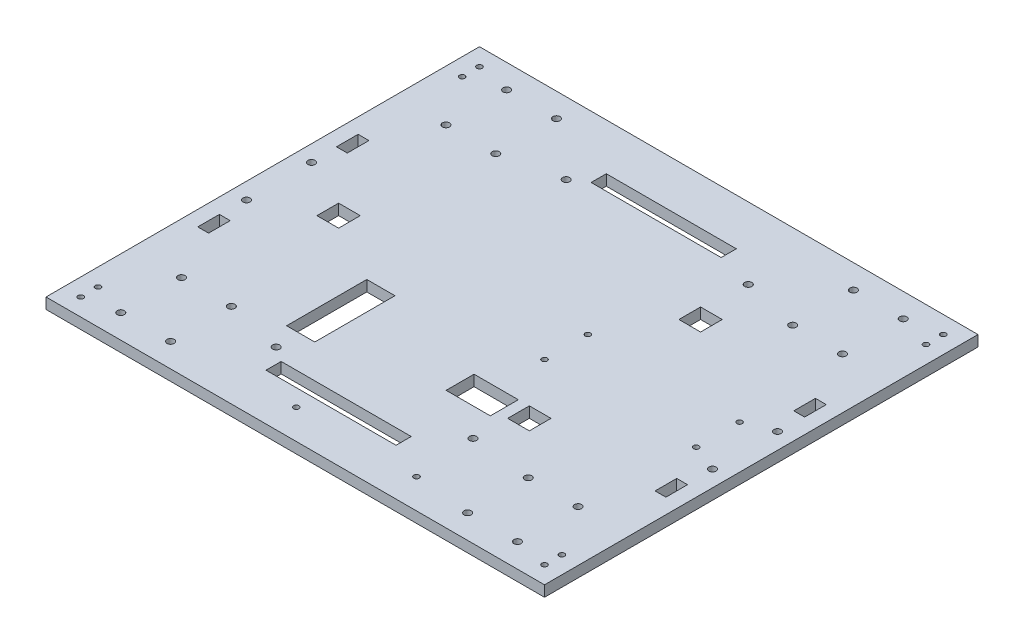
SolidWorks part; units mm, degrees
material "1060 Alloy"
ref_plane "Ebene vorne" through (0, 0, 0) normal (0, 0, 1) x (1, 0, 0)
ref_plane "Ebene oben" through (0, 0, 0) normal (0, 1, 0) x (1, 0, 0)
ref_plane "Ebene rechts" through (0, 0, 0) normal (1, 0, 0) x (0, 0, -1)
sketch "Sketch1" plane through (0, 0, 0) normal (0, 1, 0) x (1, 0, 0)
  line L1 (-110, -91.3059) -> (120, -91.3059)
  line L2 (-110, -91.3059) -> (-110, 108.6941)
  line L3 (-110, 108.6941) -> (120, 108.6941)
  line L4 (120, -91.3059) -> (120, 108.6941)
  line L5 (-110, -91.3059) -> (120, 108.6941) construction
  line L6 (-110, 108.6941) -> (120, -91.3059) construction
  point P0 (5, 8.6941)
  dimension "D1" = 200
  dimension "D2" = 230
extrude "Extrude1" add sketch "Sketch1" along normal blind 5 contours L2 L1 L4 L3
sketch "Sketch3" plane through (0, 5, 0) normal (0, 1, 0) x (1, 0, 0)
  line L0 (-110, -91.3059) -> (-110, 108.6941) construction
  line L1 (-100, 108.6941) -> (-50, 108.6941) construction
  line L2 (-100, 108.6941) -> (-100, 18.6941) construction
  line L3 (-100, 18.6941) -> (-50, 18.6941) construction
  line L4 (-50, 108.6941) -> (-50, 18.6941) construction
  line L5 (-110, 108.6941) -> (120, 108.6941) construction
  line L6 (-110, -91.3059) -> (120, -91.3059) construction
  line L7 (-100, -91.3059) -> (-50, -91.3059) construction
  line L8 (-100, -91.3059) -> (-100, -1.3059) construction
  line L9 (-100, -1.3059) -> (-50, -1.3059) construction
  line L10 (-50, -91.3059) -> (-50, -1.3059) construction
  line L11 (120, -91.3059) -> (120, 108.6941) construction
  line L12 (60, -1.3059) -> (110, -1.3059) construction
  line L13 (60, -1.3059) -> (60, -91.3059) construction
  line L14 (60, -91.3059) -> (110, -91.3059) construction
  line L15 (110, -1.3059) -> (110, -91.3059) construction
  line L17 (60, 108.6941) -> (110, 108.6941) construction
  line L18 (60, 108.6941) -> (60, 18.6941) construction
  line L19 (60, 18.6941) -> (110, 18.6941) construction
  line L20 (110, 108.6941) -> (110, 18.6941) construction
  line L21 (-95, 88.6941) -> (105, 88.6941) construction
  line L22 (-95, 88.6941) -> (-95, -71.3059) construction
  line L23 (-95, -71.3059) -> (105, -71.3059) construction
  line L24 (105, 88.6941) -> (105, -71.3059) construction
  line L29 (-30, 80.1941) -> (30, 80.1941)
  line L30 (-30, 80.1941) -> (-30, 87.1941)
  line L31 (-30, 87.1941) -> (30, 87.1941)
  line L32 (30, 80.1941) -> (30, 87.1941)
  line L33 (-30, 80.1941) -> (30, 87.1941) construction
  line L34 (-30, 87.1941) -> (30, 80.1941) construction
  line L35 (-30, -69.8059) -> (30, -69.8059)
  line L36 (-30, -69.8059) -> (-30, -62.8059)
  line L37 (-30, -62.8059) -> (30, -62.8059)
  line L38 (30, -69.8059) -> (30, -62.8059)
  line L39 (-30, -69.8059) -> (30, -62.8059) construction
  line L40 (-30, -62.8059) -> (30, -69.8059) construction
  line L41 (-43, -10.3059) -> (-30, -10.3059)
  line L42 (-43, -10.3059) -> (-43, -47.3059)
  line L43 (-43, -47.3059) -> (-30, -47.3059)
  line L44 (-30, -10.3059) -> (-30, -47.3059)
  circle A0 centre (-86.5, 97.6941) radius 1.65
  circle A1 centre (-63.5, 97.6941) radius 1.65
  circle A2 centre (-86.5, 69.6941) radius 1.65
  circle A3 centre (-63.5, 69.6941) radius 1.65
  circle A4 centre (-86.5, -52.3059) radius 1.65
  circle A5 centre (-63.5, -52.3059) radius 1.65
  circle A6 centre (-86.5, -80.3059) radius 1.65
  circle A7 centre (-63.5, -80.3059) radius 1.65
  circle A8 centre (73.5, -52.3059) radius 1.65
  circle A9 centre (96.5, -52.3059) radius 1.65
  circle A10 centre (73.5, -80.3059) radius 1.65
  circle A11 centre (96.5, -80.3059) radius 1.65
  circle A12 centre (73.5, 97.6941) radius 1.65
  circle A13 centre (96.5, 97.6941) radius 1.65
  circle A14 centre (73.5, 69.6941) radius 1.65
  circle A15 centre (96.5, 69.6941) radius 1.65
  circle A17 centre (-36.9, -58.2059) radius 1.65
  circle A18 centre (-36.9, 75.5941) radius 1.65
  circle A19 centre (47, 75.6941) radius 1.65
  circle A20 centre (45, -49.3059) radius 1.65
  point P68 (0, 83.6941)
  point P73 (0, -66.3059)
  dimension "D5" = 3.3
  dimension "D7" = 3.3
  dimension "D11" = 3.3
  dimension "D12" = 3.3
  dimension "D18" = 3.3
  dimension "D54" = 3.3
  dimension "D57" = 3.3
  dimension "D62" = 3.3
  dimension "D63" = 3.3
  dimension "D17" = 3.3
  dimension "D43" = 3.3
  dimension "D47" = 3.3
  dimension "D74" = 3.3
  dimension "D75" = 3.3
  dimension "D76" = 3.3
  dimension "D77" = 3.3
  dimension "D78" = 3.3
  dimension "D79" = 3.3
  dimension "D80" = 3.3
  dimension "D81" = 3.3
  dimension "D1" = 90
  dimension "D2" = 50
  dimension "D3" = 10
  dimension "D6" = 13.5
  dimension "D8" = 13.5
  dimension "D9" = 11
  dimension "D10" = 11
  dimension "D13" = 28
  dimension "D14" = 28
  dimension "D15" = 90
  dimension "D16" = 50
  dimension "D19" = 23
  dimension "D20" = 28
  dimension "D21" = 28
  dimension "D22" = 23
  dimension "D23" = 13.5
  dimension "D24" = 11
  dimension "D25" = 11
  dimension "D26" = 90
  dimension "D27" = 50
  dimension "D28" = 10
  dimension "D29" = 23
  dimension "D30" = 28
  dimension "D31" = 28
  dimension "D32" = 23
  dimension "D33" = 11
  dimension "D34" = 11
  dimension "D35" = 13.5
  dimension "D36" = 13.5
  dimension "D37" = 13.5
  dimension "D38" = 23
  dimension "D39" = 23
  dimension "D40" = 28
  dimension "D41" = 28
  dimension "D42" = 13.5
  dimension "D44" = 10
  dimension "D45" = 11
  dimension "D46" = 11
  dimension "D48" = 160
  dimension "D49" = 200
  dimension "D50" = 20
  dimension "D51" = 15
  dimension "D52" = 13.1
  dimension "D53" = 58.1
  dimension "D55" = 58.1
  dimension "D56" = 13.1
  dimension "D58" = 13
  dimension "D59" = 58
  dimension "D60" = 22
  dimension "D61" = 60
  dimension "D64" = 7
  dimension "D65" = 60
  dimension "D66" = 7
  dimension "D67" = 60
  dimension "D68" = 25
  dimension "D69" = 25
  dimension "D70" = 52
  dimension "D71" = 13
  dimension "D72" = 24
  dimension "D73" = 37
extrude "Extrude2" cut sketch "Sketch3" against normal blind 5
sketch "Skizze1" plane through (0, 5, 0) normal (0, 1, 0) x (1, 0, 0)
  line L1 (-110, 108.6941) -> (-88, 108.6941) construction
  line L2 (-110, 108.6941) -> (-110, 96.6941) construction
  line L3 (-110, 96.6941) -> (-88, 96.6941) construction
  line L4 (-88, 108.6941) -> (-88, 96.6941) construction
  line L5 (-110, -91.3059) -> (-88, -91.3059) construction
  line L6 (-110, -91.3059) -> (-110, -79.3059) construction
  line L7 (-110, -79.3059) -> (-88, -79.3059) construction
  line L8 (-88, -91.3059) -> (-88, -79.3059) construction
  line L9 (120, -91.3059) -> (98, -91.3059) construction
  line L10 (120, -91.3059) -> (120, -79.3059) construction
  line L11 (120, -79.3059) -> (98, -79.3059) construction
  line L12 (98, -91.3059) -> (98, -79.3059) construction
  line L13 (120, 108.6941) -> (98, 108.6941) construction
  line L14 (120, 108.6941) -> (120, 96.6941) construction
  line L15 (120, 96.6941) -> (98, 96.6941) construction
  line L16 (98, 108.6941) -> (98, 96.6941) construction
  circle A2 centre (-102, 100.6941) radius 1.25
  circle A3 centre (-102, -83.3059) radius 1.25
  circle A6 centre (112, -83.3059) radius 1.25
  circle A9 centre (112, 100.6941) radius 1.25
  circle A10 centre (-102, -75.3059) radius 1.25
  circle A11 centre (-102, 92.6941) radius 1.25
  circle A12 centre (112, 92.6941) radius 1.25
  circle A13 centre (112, -75.3059) radius 1.25
  dimension "D6" = 2.5
  dimension "D7" = 8
  dimension "D11" = 2.5
  dimension "D14" = 2.5
  dimension "D19" = 8
  dimension "D20" = 2.5
  dimension "D21" = 12
  dimension "D23" = 2.5
  dimension "D24" = 2.5
  dimension "D4" = 2.5
  dimension "D18" = 2.5
  dimension "D1" = 12
  dimension "D2" = 22
  dimension "D5" = 8
  dimension "D8" = 12
  dimension "D9" = 22
  dimension "D10" = 8
  dimension "D12" = 8
  dimension "D13" = 8
  dimension "D15" = 22
  dimension "D16" = 12
  dimension "D17" = 8
  dimension "D22" = 22
  dimension "D25" = 8
  dimension "D26" = 8
  dimension "D28" = 8
  dimension "D31" = 8
extrude "Schnitt-Linear austragen1" cut sketch "Skizze1" against normal blind 10
sketch "Skizze3" plane through (0, 5, 0) normal (0, 1, 0) x (1, 0, 0)
  line L5 (-15.4717, -87.6433) -> (54.5283, -87.6433)
  line L6 (-15.4717, -87.6433) -> (-15.4717, -72.6433)
  line L7 (-15.4717, -72.6433) -> (54.5283, -72.6433)
  line L8 (54.5283, -87.6433) -> (54.5283, -72.6433)
  circle A2 centre (-8.2217, -77.6433) radius 1.25
  circle A3 centre (47.2783, -77.6433) radius 1.25
  dimension "D14" = 2.5
  dimension "D8" = 15
  dimension "D9" = 70
  dimension "D10" = 5
  dimension "D11" = 5
  dimension "D12" = 7.25
  dimension "D13" = 7.25
extrude "Schnitt-Linear austragen3" cut sketch "Skizze3" against normal blind 5 contours A2 | A3
sketch "Skizze4" plane through (0, 5, 0) normal (0, 1, 0) x (1, 0, 0)
  line L0 (-110, 108.6941) -> (120, 108.6941) construction
  line L1 (105, -31.3059) -> (120, -31.3059) construction
  line L2 (105, -31.3059) -> (105, 48.6941) construction
  line L3 (105, 48.6941) -> (120, 48.6941) construction
  line L4 (120, -31.3059) -> (120, 48.6941) construction
  line L5 (105, -31.3059) -> (120, 48.6941) construction
  line L6 (105, 48.6941) -> (120, -31.3059) construction
  line L8 (120, -91.3059) -> (120, 108.6941) construction
  line L9 (-110, -91.3059) -> (-110, 108.6941) construction
  line L10 (-110, -31.3059) -> (-95, -31.3059) construction
  line L11 (-110, -31.3059) -> (-110, 48.6941) construction
  line L12 (-110, 48.6941) -> (-95, 48.6941) construction
  line L13 (-95, -31.3059) -> (-95, 48.6941) construction
  line L14 (-110, -31.3059) -> (-95, 48.6941) construction
  line L15 (-110, 48.6941) -> (-95, -31.3059) construction
  line L17 (108, -28.3059) -> (113, -28.3059)
  line L18 (108, -28.3059) -> (108, -18.3059)
  line L19 (108, -18.3059) -> (113, -18.3059)
  line L20 (113, -28.3059) -> (113, -18.3059)
  line L21 (108, 45.6941) -> (113, 45.6941)
  line L22 (108, 45.6941) -> (108, 35.6941)
  line L23 (108, 35.6941) -> (113, 35.6941)
  line L24 (113, 45.6941) -> (113, 35.6941)
  line L25 (-98, 45.6941) -> (-103, 45.6941)
  line L26 (-98, 45.6941) -> (-98, 35.6941)
  line L27 (-98, 35.6941) -> (-103, 35.6941)
  line L28 (-103, 45.6941) -> (-103, 35.6941)
  line L29 (-98, -28.3059) -> (-103, -28.3059)
  line L30 (-98, -28.3059) -> (-98, -18.3059)
  line L31 (-98, -18.3059) -> (-103, -18.3059)
  line L32 (-103, -28.3059) -> (-103, -18.3059)
  circle A0 centre (112.5, 23.6941) radius 1.65
  circle A1 centre (112.5, -6.3059) radius 1.65
  circle A2 centre (-102.5, 23.6941) radius 1.65
  circle A3 centre (-102.5, -6.3059) radius 1.65
  point P0 (112.5, 8.6941)
  point P15 (-102.5, 8.6941)
  dimension "D6" = 3.3
  dimension "D11" = 3.3
  dimension "D1" = 15
  dimension "D2" = 80
  dimension "D3" = 100
  dimension "D4" = 15
  dimension "D5" = 15
  dimension "D7" = 7.5
  dimension "D8" = 80
  dimension "D9" = 15
  dimension "D10" = 7.5
  dimension "D12" = 3
  dimension "D13" = 3
  dimension "D14" = 5
  dimension "D15" = 10
  dimension "D16" = 3
  dimension "D17" = 3
  dimension "D18" = 10
  dimension "D19" = 3
  dimension "D20" = 3
  dimension "D21" = 5
  dimension "D22" = 10
  dimension "D23" = 5
  dimension "D24" = 5
  dimension "D25" = 3
  dimension "D26" = 3
  dimension "D27" = 10
extrude "Schnitt-Linear austragen4" cut sketch "Skizze4" against normal blind 10
sketch "Skizze5" plane through (0, 5, 0) normal (0, 1, 0) x (1, 0, 0)
  line L1 (-110, 108.6941) -> (120, 108.6941) construction
  line L2 (120, -91.3059) -> (120, 108.6941) construction
  circle A0 centre (100, 18.6941) radius 1.25
  circle A1 centre (100, -1.3059) radius 1.25
  circle A2 centre (30, 18.6941) radius 1.25
  circle A3 centre (30, -1.3059) radius 1.25
  dimension "D5" = 2.5
  dimension "D6" = 90
  dimension "D1" = 70
  dimension "D2" = 70
  dimension "D3" = 20
  dimension "D4" = 20
  dimension "D7" = 20
extrude "Schnitt-Linear austragen5" cut sketch "Skizze5" against normal blind 10
sketch "Skizze6" plane through (0, 5, 0) normal (0, 1, 0) x (1, 0, 0)
  line L0 (-110, -91.3059) -> (120, -91.3059) construction
  line L1 (19.6, -23.4059) -> (40, -23.4059)
  line L2 (19.6, -23.4059) -> (19.6, -36.3059)
  line L3 (19.6, -36.3059) -> (40, -36.3059)
  line L4 (40, -23.4059) -> (40, -36.3059)
  line L5 (120, -91.3059) -> (120, 108.6941) construction
  dimension "D1" = 12.9
  dimension "D2" = 20.4
  dimension "D3" = 55
  dimension "D4" = 80
extrude "Schnitt-Linear austragen6" cut sketch "Skizze6" against normal blind 10
sketch "Skizze7" plane through (0, 5, 0) normal (0, 1, 0) x (1, 0, 0)
  line L0 (-80, 13.6941) -> (-70, 3.6941) construction
  line L1 (-80, 13.6941) -> (-70, 13.6941)
  line L2 (-80, 13.6941) -> (-80, 3.6941)
  line L3 (-80, 3.6941) -> (-70, 3.6941)
  line L4 (-70, 13.6941) -> (-70, 3.6941)
  line L5 (-70, 13.6941) -> (-80, 3.6941) construction
  line L6 (-110, -91.3059) -> (120, -91.3059) construction
  circle A2 centre (-86.5, 69.6941) radius 1.65 construction
  point P4 (-75, 8.6941)
  dimension "D4" = 11.5
  dimension "D1" = 10
  dimension "D2" = 10
  dimension "D3" = 100
extrude "Schnitt-Linear austragen7" cut sketch "Skizze7" against normal blind 10
sketch "Skizze8" plane through (0, 5, 0) normal (0, 1, 0) x (1, 0, 0)
  line L0 (120, -91.3059) -> (120, 108.6941) construction
  line L1 (45, 55.6941) -> (55, 55.6941)
  line L2 (45, 55.6941) -> (45, 45.6941)
  line L3 (45, 45.6941) -> (55, 45.6941)
  line L4 (55, 55.6941) -> (55, 45.6941)
  line L5 (45, -23.3059) -> (55, -23.3059)
  line L6 (45, -23.3059) -> (45, -33.3059)
  line L7 (45, -33.3059) -> (55, -33.3059)
  line L8 (55, -23.3059) -> (55, -33.3059)
  line L10 (-110, -91.3059) -> (120, -91.3059) construction
  line L11 (-110, 108.6941) -> (120, 108.6941) construction
  dimension "D1" = 10
  dimension "D2" = 10
  dimension "D3" = 10
  dimension "D4" = 10
  dimension "D5" = 65
  dimension "D6" = 65
  dimension "D7" = 58
  dimension "D8" = 53
extrude "Schnitt-Linear austragen8" cut sketch "Skizze8" against normal blind 10
